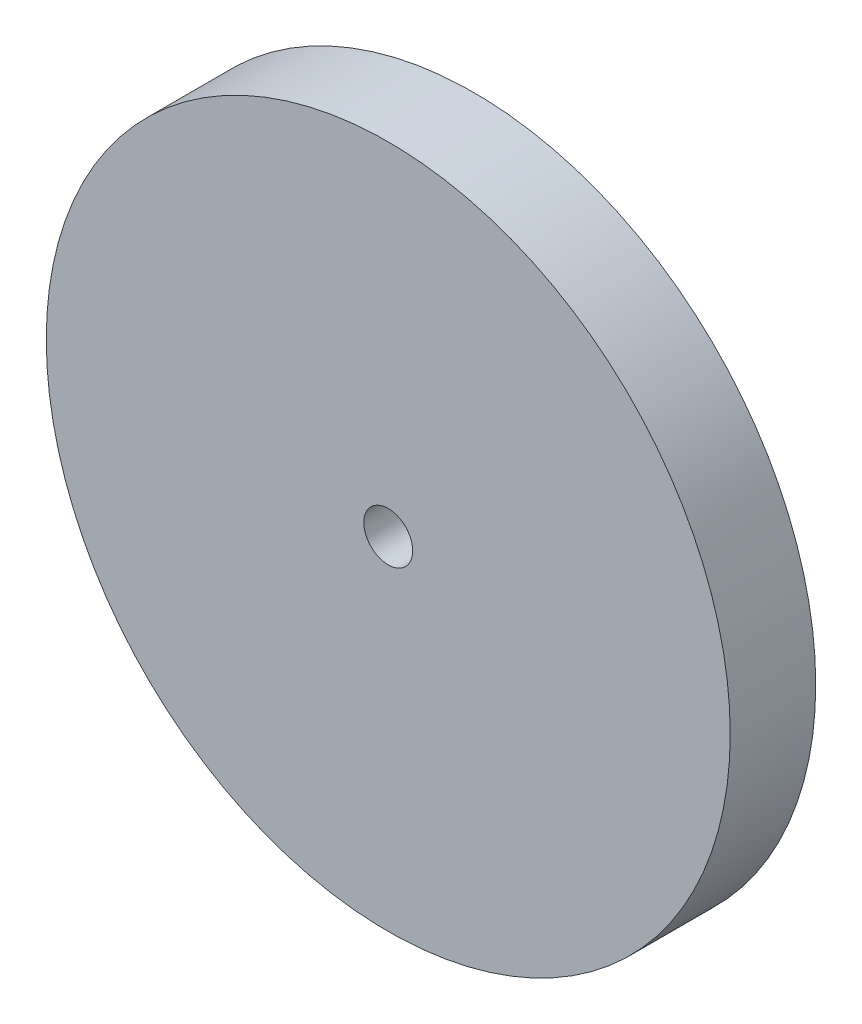
SolidWorks part; units mm, degrees
ref_plane "Front Plane" through (0, 0, 0) normal (0, 0, 1) x (1, 0, 0)
ref_plane "Top Plane" through (0, 0, 0) normal (0, 1, 0) x (1, 0, 0)
ref_plane "Right Plane" through (0, 0, 0) normal (1, 0, 0) x (0, 0, -1)
sketch "Sketch1" plane through (0, 0, 0) normal (0, 0, 1) x (1, 0, 0)
  circle A0 centre (0, 0) radius 14
  circle A1 centre (0, 0) radius 1
  dimension "D1" = 28
  dimension "D2" = 2
extrude "Boss-Extrude1" add sketch "Sketch1" along normal blind 3.5
